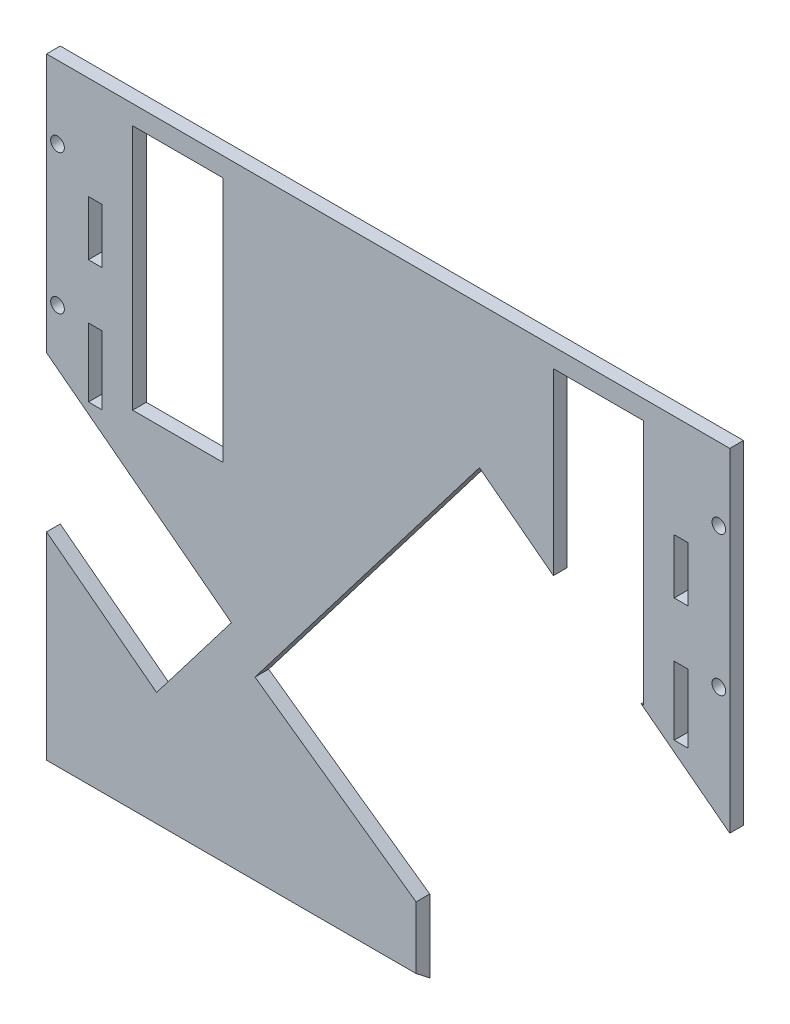
SolidWorks part; units mm, degrees
ref_plane "Front Plane" through (0, 0, 0) normal (0, 0, 1) x (1, 0, 0)
ref_plane "Top Plane" through (0, 0, 0) normal (0, 1, 0) x (1, 0, 0)
ref_plane "Right Plane" through (0, 0, 0) normal (1, 0, 0) x (0, 0, -1)
sketch "Sketch1" plane through (0, 0, 0) normal (0, 0, 1) x (1, 0, 0)
  line L0 (124.8, 0) -> (124.8, -284.42) construction
  line L1 (0, 0) -> (249.6, 0)
  line L2 (0, 0) -> (0, -284.42)
  line L3 (0, -284.42) -> (249.6, -284.42)
  line L4 (249.6, 0) -> (249.6, -284.42)
  line L9 (185.16, -7) -> (218.16, -7)
  line L10 (185.16, -7) -> (185.16, -97)
  line L11 (185.16, -97) -> (218.16, -97)
  line L12 (218.16, -7) -> (218.16, -97)
  line L52 (204.16, -7) -> (204.16, -97) construction
  line L53 (194.16, -7) -> (214.16, -7) construction
  line L54 (194.16, -7) -> (194.16, -97) construction
  line L55 (194.16, -97) -> (214.16, -97) construction
  line L56 (214.16, -7) -> (214.16, -97) construction
  line L102 (245.6, -26.5) -> (245.6, -77.5) construction
  line L103 (218.16, -52) -> (245.6, -52) construction
  line L134 (31.44, -52) -> (4, -52) construction
  line L135 (4, -26.5) -> (4, -77.5) construction
  line L139 (35.44, -7) -> (35.44, -97) construction
  line L140 (55.44, -97) -> (35.44, -97) construction
  line L141 (55.44, -7) -> (55.44, -97) construction
  line L142 (55.44, -7) -> (35.44, -7) construction
  line L143 (45.44, -7) -> (45.44, -97) construction
  line L154 (31.44, -7) -> (31.44, -97)
  line L155 (64.44, -97) -> (31.44, -97)
  line L156 (64.44, -7) -> (64.44, -97)
  line L157 (64.44, -7) -> (31.44, -7)
  circle A84 centre (245.6, -26.5) radius 2.5
  circle A85 centre (245.6, -77.5) radius 2.5
  circle A236 centre (4, -77.5) radius 2.5
  circle A237 centre (4, -26.5) radius 2.5
  dimension "D5" = 20
  dimension "D15" = 5
  dimension "D16" = 5
  dimension "D1" = 249.6
  dimension "D2" = 284.42
  dimension "D3" = 4
  dimension "D4" = 90
  dimension "D6" = 90
  dimension "D7" = 9
  dimension "D8" = 7
  dimension "D14" = 89.36
  dimension "D17" = 25.5
  dimension "D18" = 4
extrude "Boss-Extrude1" add sketch "Sketch1" along normal blind 5
sketch "Sketch2" plane through (0, 0, 5) normal (0, 0, 1) x (1, 0, 0)
  line L0 (-12.0438, -116.1701) -> (14.8299, 12.0438) construction
  line L1 (357.917, -193.7139) -> (384.7906, -65.5) construction
  line L2 (-12.0438, -116.1701) -> (357.917, -193.7139) construction
  line L3 (28.6688, 50.2813) -> (25.735, 46.2325) construction
  line L4 (25.735, 46.2325) -> (79.8591, 7.0134) construction
  line L5 (89.8056, 5.9807) -> (28.6688, 50.2813) construction
  line L6 (14.8299, 12.0438) -> (384.7906, -65.5) construction
  line L7 (14.2144, 9.1076) -> (384.1752, -68.4362) construction
  line L8 (-11.4283, -113.2339) -> (358.5324, -190.7777) construction
  line L9 (28.6688, 50.2813) -> (31.6026, 54.33) construction
  line L10 (31.6026, 54.33) -> (85.7267, 15.111) construction
  line L11 (236.1909, -165.1349) -> (261.8337, -42.7934) construction
  line L12 (126.6708, -78.3214) -> (249.0123, -103.9642) construction
  line L13 (113.8494, -139.4922) -> (139.4922, -17.1506) construction
  line L14 (249.6, 0) -> (0, 0) construction
  line L15 (0, 0) -> (0, -284.42) construction
  circle A0 centre (65.5, -65.5) radius 62.5 construction
  circle A1 centre (310.183, -116.7856) radius 62.5 construction
  circle A2 centre (65.5, -65.5) radius 65.5 construction
  circle A3 centre (187.8415, -91.1428) radius 62.5 construction
  circle A4 centre (89.8056, 5.9807) radius 75.5 construction
  circle A5 centre (89.8056, 5.9807) radius 2.5 construction
  circle A6 centre (69.5617, 20.6497) radius 1.5 construction
  arc A7 (79.8591, 7.0134) -> (85.7267, 15.111) centre (89.8056, 5.9807) ccw construction
  dimension "D1" = 125
  dimension "D2" = 125
  dimension "D3" = 5
  dimension "D6" = 3
  dimension "D7" = 10
  dimension "D10" = 125
  dimension "D8" = 3
  dimension "D4" = 5
  dimension "D5" = 25
  dimension "D9" = 5
ref_plane "Plane1"
sketch "Sketch4" plane through (0, -141.1875, 110.3078) normal (0, 0.788, -0.6157) x (1, 0, 0)
  line L0 (0, 206.4003) -> (135, 206.4003)
  line L1 (0, 206.4003) -> (0, -38.0664)
  line L2 (135, 206.4003) -> (135, -38.0664)
  line L3 (0, -38.0664) -> (135, -38.0664)
  line L4 (0, 253.2196) -> (0, 43.3406) construction
  line L5 (0, -22.0114) -> (0, 37.0155) construction
  line L6 (135, 253.2196) -> (135, 43.3406) construction
extrude "Cut-Extrude2" cut sketch "Sketch4" against normal through all
sketch "Sketch5" plane through (0, 0, 5) normal (0, 0, 1) x (1, 0, 0)
  line L0 (76.1492, -159.0843) -> (158.1494, -51.8418)
  line L1 (135, -284.42) -> (207.3188, -339.7167)
  line L2 (158.1494, -51.8418) -> (328.0831, -181.7773)
  line L3 (207.3188, -339.7167) -> (328.0831, -181.7773)
  line L4 (79.1862, -155.1124) -> (155.1124, -55.8138) construction
  line L5 (76.1492, -159.0843) -> (135, -200.789)
  line L6 (54.8789, 27.1214) -> (359.1299, -205.5164) construction
  line L7 (135, -200.789) -> (135, -284.42)
  line L8 (135, -284.42) -> (135, -223.463) construction
extrude "Cut-Extrude3" cut sketch "Sketch5" against normal through all
sketch "Sketch6" plane through (0, 0, 5) normal (0, 0, 1) x (1, 0, 0)
  line L0 (0, -94.5647) -> (67.5231, -146.1945)
  line L1 (0, -94.5647) -> (-27.3334, -130.3122)
  line L2 (67.5231, -146.1945) -> (40.1896, -181.942)
  line L3 (-27.3334, -130.3122) -> (40.1896, -181.942)
  line L4 (0, 0) -> (0, -223.463) construction
  line L5 (-24.0843, -76.1492) -> (280.1666, -308.787) construction
  dimension "D1" = 85
  dimension "D2" = 45
extrude "Cut-Extrude4" cut sketch "Sketch6" against normal through all
sketch "Sketch7" plane through (0, 0, 5) normal (0, 0, 1) x (1, 0, 0)
  line L0 (124.8, 45.2798) -> (124.8, -137.1886) construction
  line L18 (15.2882, -37.4779) -> (20.2882, -37.4779)
  line L19 (15.2882, -37.4779) -> (15.2882, -57.4779)
  line L23 (15.2882, -57.4779) -> (20.2882, -57.4779)
  line L24 (20.2882, -37.4779) -> (20.2882, -57.4779)
  line L25 (229.3118, -37.4779) -> (234.3118, -37.4779)
  line L26 (229.3118, -37.4779) -> (229.3118, -57.4779)
  line L27 (229.3118, -57.4779) -> (234.3118, -57.4779)
  line L28 (234.3118, -37.4779) -> (234.3118, -57.4779)
  line L29 (15.2882, -77.4779) -> (20.2882, -77.4779)
  line L30 (15.2882, -77.4779) -> (15.2882, -102.4779)
  line L31 (15.2882, -102.4779) -> (20.2882, -102.4779)
  line L32 (20.2882, -77.4779) -> (20.2882, -102.4779)
  line L33 (229.3118, -77.4779) -> (234.3118, -77.4779)
  line L34 (229.3118, -77.4779) -> (229.3118, -102.4779)
  line L35 (229.3118, -102.4779) -> (234.3118, -102.4779)
  line L36 (234.3118, -77.4779) -> (234.3118, -102.4779)
  line L37 (17.7882, -37.4779) -> (17.7882, -111.359) construction
  line L38 (231.8118, -37.4779) -> (231.8118, -111.6165) construction
  line L39 (0, 0) -> (0, -94.5647) construction
  line L40 (249.6, -121.7672) -> (249.6, 0) construction
  line L42 (249.6, -121.7672) -> (217.2087, -97) construction
  line L43 (67.5231, -146.1945) -> (0, -94.5647) construction
  dimension "D1" = 5
  dimension "D2" = 20
  dimension "D3" = 5
  dimension "D4" = 20
  dimension "D5" = 5
  dimension "D6" = 25
  dimension "D7" = 5
  dimension "D8" = 25
  dimension "D9" = 20
  dimension "D10" = 20
  dimension "D11" = 3
  dimension "D12" = 3
extrude "Cut-Extrude5" cut sketch "Sketch7" against normal through all
